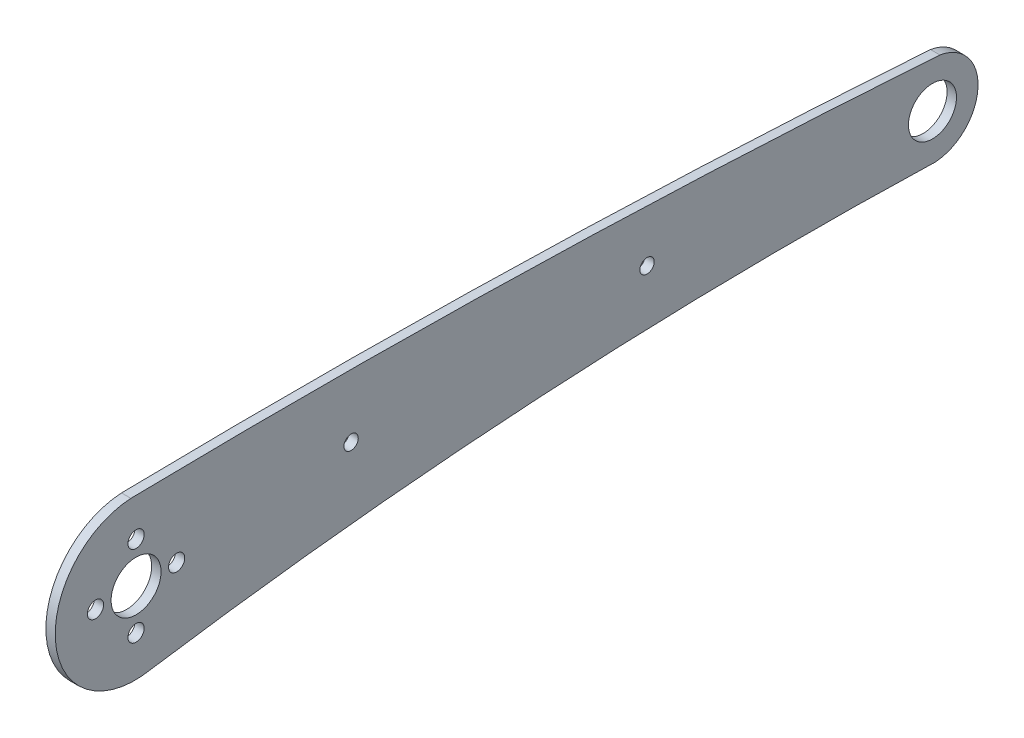
SolidWorks part; units mm, degrees
ref_plane "前基準面" through (0, 0, 0) normal (0, 0, 1) x (1, 0, 0)
ref_plane "上基準面" through (0, 0, 0) normal (0, 1, 0) x (1, 0, 0)
ref_plane "右基準面" through (0, 0, 0) normal (1, 0, 0) x (0, 0, -1)
sketch "草圖1" plane through (0, 0, 0) normal (1, 0, 0) x (0, 0, -1)
  circle A0 centre (-67.4697, 0.0796) radius 1.3
  circle A1 centre (-54.4697, 0.0796) radius 1.3
  circle A2 centre (-60.9697, 6.5796) radius 1.3
  circle A3 centre (-60.9697, -6.4204) radius 1.3
  circle A6 centre (66.6171, 2.1616) radius 3.85
  circle A7 centre (-60.9697, 0.0796) radius 4
  circle A8 centre (20.8921, 3.5712) radius 1.149
  circle A9 centre (-26.5219, 2.7975) radius 1.149
  arc A10 (66.5877, -5.1166) -> (-58.6335, -12.6811) centre (45.4653, -695.6897) ccw
  arc A11 (-61.804, 12.6555) -> (-58.6335, -12.6811) centre (-61.1216, -0.1258) ccw
  arc A12 (66.5877, -5.1166) -> (67.0956, -5.1266) centre (66.9001, -2.1485) ccw
  arc A13 (67.0956, -5.1266) -> (67.7985, 9.3693) centre (66.6171, 2.1616) ccw
  arc A14 (67.7985, 9.3693) -> (-61.804, 12.6555) centre (-33.8038, -1440.3614) ccw
  dimension "D1" = 7.7
  dimension "D3" = 6.5
  dimension "D2" = 127.5868
extrude "填料-伸長1" add sketch "草圖1" along normal blind 1.5
